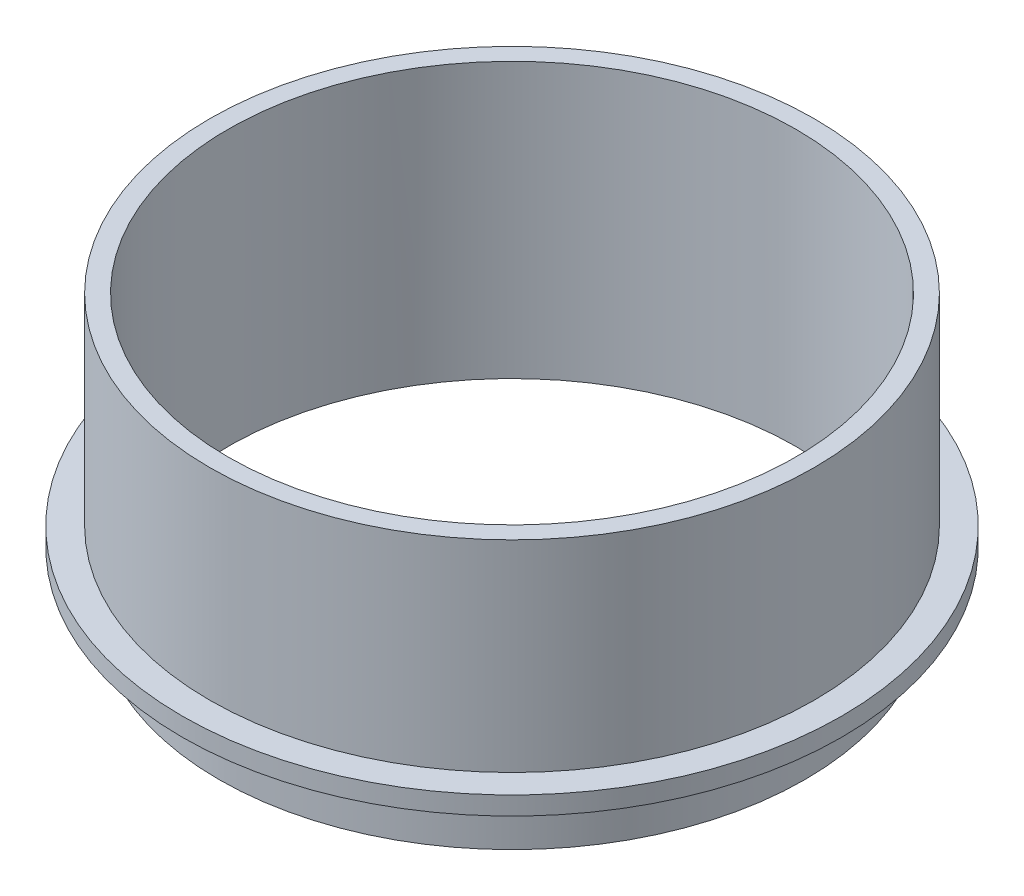
SolidWorks part; units mm, degrees
ref_plane "Front Plane" through (0, 0, 0) normal (0, 0, 1) x (1, 0, 0)
ref_plane "Top Plane" through (0, 0, 0) normal (0, 1, 0) x (1, 0, 0)
ref_plane "Right Plane" through (0, 0, 0) normal (1, 0, 0) x (0, 0, -1)
sketch "Sketch1" plane through (0, 0, 0) normal (0, 1, 0) x (1, 0, 0)
  circle A0 centre (0, 0) radius 49.2125
  circle A1 centre (0, 0) radius 52.3875
  dimension "D1" = 98.425
  dimension "D2" = 104.775
extrude "Boss-Extrude1" add sketch "Sketch1" along normal blind 38.1 contours A1 A0
sketch "Sketch2" plane through (0, 0, 0) normal (0, -1, 0) x (1, 0, 0)
  circle A0 centre (0, 0) radius 50.8
  circle A1 centre (0, 0) radius 49.2125
  circle M2 centre (0, 0) radius 49.2125
  dimension "D1" = 101.6
  dimension "D2" = 98.425
extrude "Boss-Extrude2" add sketch "Sketch2" along normal blind 9.525 contours A0 M2
sketch "Sketch3" plane through (0, 0, 0) normal (0, -1, 0) x (1, 0, 0)
  circle A0 centre (0, 0) radius 57.15
  circle A1 centre (0, 0) radius 52.3875 construction
  circle A2 centre (0, 0) radius 52.3875
  circle M2 centre (0, 0) radius 52.3875
  dimension "D1" = 114.3
extrude "Boss-Extrude3" add sketch "Sketch3" against normal blind 3.175 contours A0 M2
